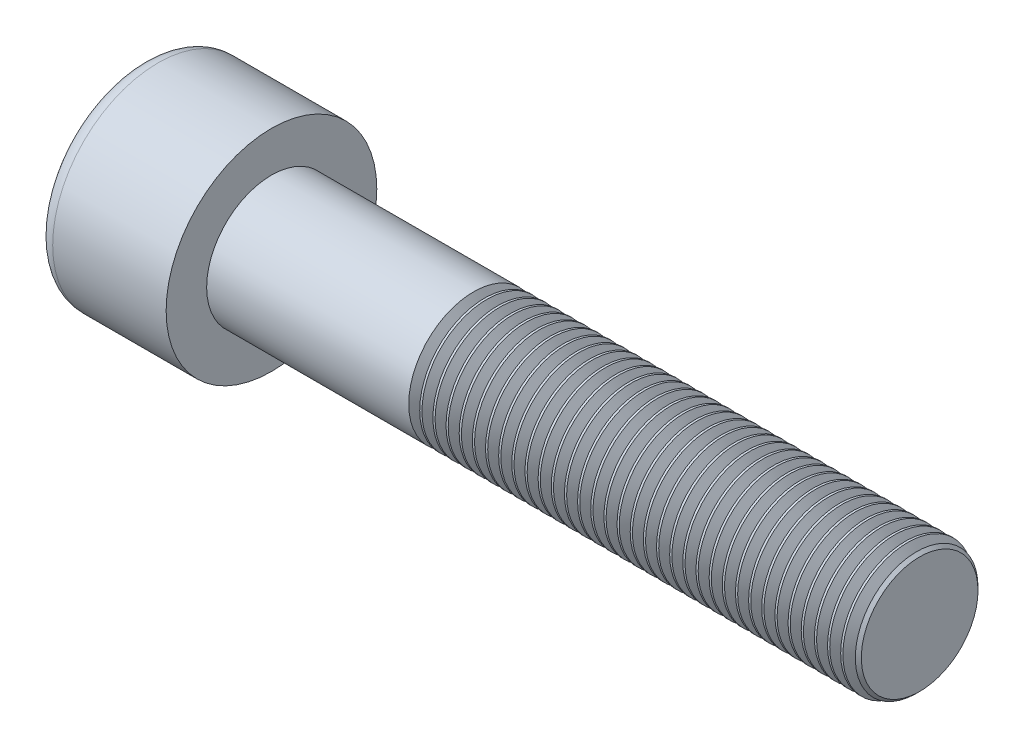
SolidWorks part; units mm, degrees
ref_plane "Front" through (0, 0, 0) normal (0, 0, 1) x (1, 0, 0)
ref_plane "Top" through (0, 0, 0) normal (0, 1, 0) x (1, 0, 0)
ref_plane "Right" through (0, 0, 0) normal (1, 0, 0) x (0, 0, -1)
sketch "Sketch1" plane through (0, 0, 0) normal (1, 0, 0) x (0, 0, -1)
  circle A0 centre (0, 0) radius 6.5
  dimension "dk" = 13
extrude "BaseHead" add sketch "Sketch1" along normal blind 8
sketch "Sketch2" plane through (8, 0, 0) normal (1, 0, 0) x (0, 0, -1)
  circle A0 centre (0, 0) radius 4
  dimension "d" = 8
extrude "BaseBody" add sketch "Sketch2" along normal blind 40
cosmetic thread "ThreadCosmetic1" [suppressed] parameters "b"=28, "D2"=6.647
sketch "Sketch3" plane through (0, 0, 0) normal (1, 0, 0) x (0, 0, -1)
  line L1 (3.4641, 0) -> (1.7321, 3)
  line L2 (1.7321, 3) -> (-1.7321, 3)
  line L3 (-1.7321, 3) -> (-3.4641, 0)
  line L4 (-3.4641, 0) -> (-1.7321, -3)
  line L5 (-1.7321, -3) -> (1.7321, -3)
  line L6 (1.7321, -3) -> (3.4641, 0)
  circle A0 centre (0, 0) radius 3 construction
  dimension "s" = 6
  dimension "e" = 6.9282
extrude "HexagonSocket" cut sketch "Sketch3" along normal blind 4
sketch "Sketch4" plane through (-4.1961, 0.75, 0) normal (0, 0, 1) x (-1, 0, 0)
  line L0 (-8.1961, 3.75) -> (-9.9282, 0.75)
  line L2 (-9.9282, 0.75) -> (-8.1961, 0.75)
  line L3 (-8.1961, 0.75) -> (-8.1961, 3.75)
  line L4 (-5.0351, 0.75) -> (0.839, 0.75) construction
  line L5 (-52.1961, 0.75) -> (-12.1961, 0.75) construction
  line L6 (-12.1961, 0.75) -> (-4.1961, 0.75) construction
  dimension "m" = 60
revolve "Cut-Revolve1" cut sketch "Sketch4" angle 360 about L4
fillet "HeadFillet" [suppressed] radius 0.4
fillet "TopFillet" radius 1 1 edges at (0, 0, -6.5)
chamfer "Chamfer1" distance 0.4 angle 45 1 edges at (48, 0, -4)
sketch "Sketch5" plane through (0, 0, 0) normal (0, 0, 1) x (1, 0, 0)
  line L0 (47.6, 3.4141) -> (47.9383, 4)
  line L1 (47.9383, 4) -> (47.9383, 4.6765)
  line L2 (47.9383, 4.6765) -> (47.2618, 4.6765)
  line L3 (47.2618, 4.6765) -> (47.2618, 4)
  line L4 (47.2618, 4) -> (47.6, 3.4141)
  line L5 (0, 0) -> (7.8886, 0) construction
  line L6 (47.6, -4) -> (47.6, 4) construction
  dimension "D1" = 8
  dimension "D2" = 0.6765
revolve "Cut-Revolve10" cut sketch "Sketch5" angle 360 about L5
pattern_linear "LPattern10" count 34 spacing 0.8118 along (-1, 0, 0) of "Cut-Revolve10"
equation "\"r1@TopFillet\" = \"d@Sketch2\" / 8"
equation "\"D1@Chamfer1\" = \"r@HeadFillet\""
equation "\"D1@Sketch5\" = \"d@Sketch2\""
equation "\"D2@Sketch5\" =  ( \"d@Sketch2\" - \"D2@ThreadCosmetic1\" )  / 2"
equation "\"D3@LPattern10\" = \"D2@Sketch5\" * 1.2"
equation "\"D1@LPattern10\" = \"b@ThreadCosmetic1\" / \"D3@LPattern10\""
